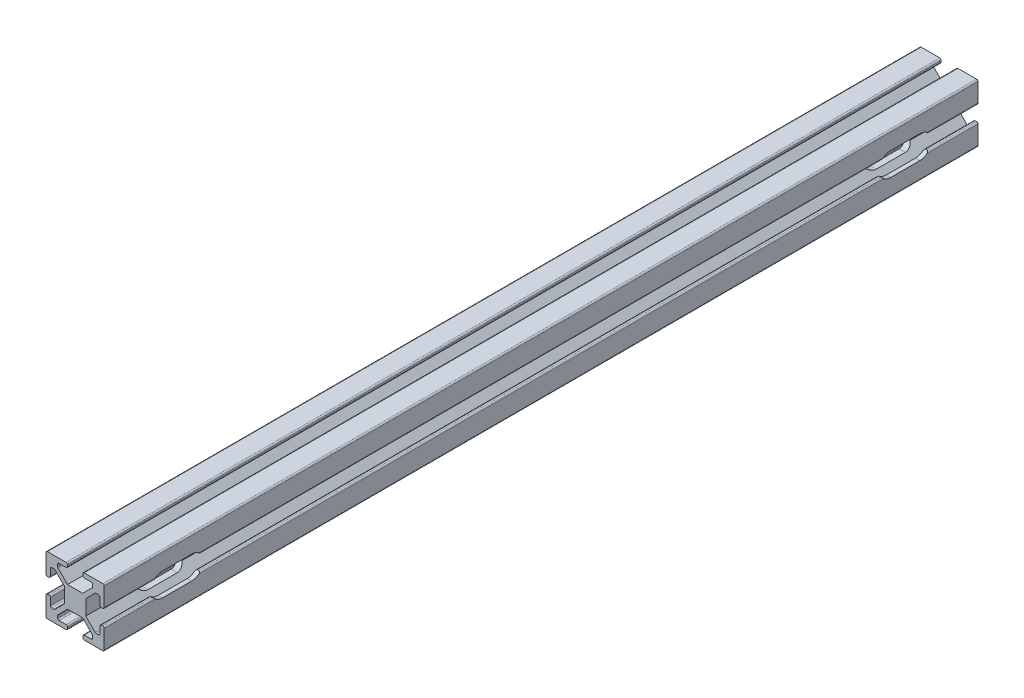
SolidWorks part; units mm, degrees
material "6061 Alloy"
ref_plane "Front Plane" through (0, 0, 0) normal (0, 0, 1) x (1, 0, 0)
ref_plane "Top Plane" through (0, 0, 0) normal (0, 1, 0) x (1, 0, 0)
ref_plane "Right Plane" through (0, 0, 0) normal (1, 0, 0) x (0, 0, -1)
sketch "Sketch1" plane through (0, 0, 0) normal (0, 0, 1) x (1, 0, 0)
  line L0 (-10, 2.63) -> (-10, 10)
  line L1 (-10, 10) -> (-2.63, 10)
  line L2 (-2.63, 10) -> (-2.63, 8.5)
  line L3 (-2.63, 8.5) -> (-5.995, 8.5)
  line L4 (-5.995, 8.5) -> (-5.995, 7.0557)
  line L5 (-5.995, 7.0557) -> (-2.5943, 3.655)
  line L6 (-2.5943, 3.655) -> (2.5943, 3.655)
  line L7 (0, 3.655) -> (0, 0) construction
  line L8 (0, 0) -> (-3.655, 0) construction
  line L9 (-3.655, -2.5943) -> (-3.655, 2.5943)
  line L10 (-3.655, 2.5943) -> (-7.0557, 5.995)
  line L11 (-7.0557, 5.995) -> (-8.5, 5.995)
  line L12 (-8.5, 5.995) -> (-8.5, 2.63)
  line L13 (-8.5, 2.63) -> (-10, 2.63)
  line L14 (8.5, 2.63) -> (10, 2.63)
  line L15 (8.5, 5.995) -> (8.5, 2.63)
  line L16 (7.0557, 5.995) -> (8.5, 5.995)
  line L17 (3.655, 2.5943) -> (7.0557, 5.995)
  line L18 (3.655, -2.5943) -> (3.655, 2.5943)
  line L19 (5.995, 7.0557) -> (2.5943, 3.655)
  line L20 (5.995, 8.5) -> (5.995, 7.0557)
  line L21 (2.63, 8.5) -> (5.995, 8.5)
  line L22 (2.63, 10) -> (2.63, 8.5)
  line L23 (10, 10) -> (2.63, 10)
  line L24 (10, 2.63) -> (10, 10)
  line L25 (10, -2.63) -> (10, -10)
  line L26 (10, -10) -> (2.63, -10)
  line L27 (2.63, -10) -> (2.63, -8.5)
  line L28 (2.63, -8.5) -> (5.995, -8.5)
  line L29 (5.995, -8.5) -> (5.995, -7.0557)
  line L30 (5.995, -7.0557) -> (2.5943, -3.655)
  line L31 (3.655, -2.5943) -> (7.0557, -5.995)
  line L32 (7.0557, -5.995) -> (8.5, -5.995)
  line L33 (8.5, -5.995) -> (8.5, -2.63)
  line L34 (8.5, -2.63) -> (10, -2.63)
  line L35 (-8.5, -2.63) -> (-10, -2.63)
  line L36 (-8.5, -5.995) -> (-8.5, -2.63)
  line L37 (-7.0557, -5.995) -> (-8.5, -5.995)
  line L38 (-3.655, -2.5943) -> (-7.0557, -5.995)
  line L39 (-2.5943, -3.655) -> (2.5943, -3.655)
  line L40 (-5.995, -7.0557) -> (-2.5943, -3.655)
  line L41 (-5.995, -8.5) -> (-5.995, -7.0557)
  line L42 (-2.63, -8.5) -> (-5.995, -8.5)
  line L43 (-2.63, -10) -> (-2.63, -8.5)
  line L44 (-10, -10) -> (-2.63, -10)
  line L45 (-10, -2.63) -> (-10, -10)
  point P41 (3.655, 0)
  dimension "D1" = 20
  dimension "D2" = 20
  dimension "D3" = 5.26
  dimension "D4" = 11.99
  dimension "D5" = 1.5
  dimension "D6" = 1.5
  dimension "D7" = 7.31
extrude "Boss-Extrude1" add sketch "Sketch1" against normal blind 300
fillet "Fillet1" radius 0.5 36 edges at (10, 10, -150) (7.0557, 5.995, -150) (8.5, 2.63, -150) (10, 2.63, -150) (8.5, 5.995, -150) (2.63, 10, -150) (2.63, 8.5, -150) (5.995, 8.5, -150) (5.995, 7.0557, -150) (10, -10, -150) (10, -2.63, -150) (8.5, -2.63, -150) (8.5, -5.995, -150) (7.0557, -5.995, -150) (5.995, -7.0557, -150) (5.995, -8.5, -150) (2.63, -8.5, -150) (2.63, -10, -150) (-10, -10, -150) (-2.63, -10, -150) (-2.63, -8.5, -150) (-5.995, -8.5, -150) (-5.995, -7.0557, -150) (-7.0557, -5.995, -150) (-8.5, -5.995, -150) (-10, -2.63, -150) (-8.5, -2.63, -150) (-7.0557, 5.995, -150) (-10, 10, -150) (-10, 2.63, -150) (-8.5, 2.63, -150) (-8.5, 5.995, -150) (-5.995, 8.5, -150) (-5.995, 7.0557, -150) (-2.63, 8.5, -150) (-2.63, 10, -150)
sketch "Sketch2" plane through (0, 0, 0) normal (1, 0, 0) x (0, 0, -1)
  line L0 (150, 9.5) -> (150, -9.5) construction
  line L1 (300, 9.5) -> (0, 9.5) construction
  line L2 (0, -9.5) -> (300, -9.5) construction
  line L3 (20, 4) -> (30, 4)
  line L4 (20, -4) -> (30, -4)
  line L5 (280, 4) -> (270, 4)
  line L6 (280, -4) -> (270, -4)
  arc A0 (20, 4) -> (20, -4) centre (20, 0) ccw
  arc A2 (30, -4) -> (30, 4) centre (30, 0) ccw
  arc A3 (280, 4) -> (280, -4) centre (280, 0) cw
  arc A4 (270, -4) -> (270, 4) centre (270, 0) cw
  dimension "D1" = 8
  dimension "D2" = 20
  dimension "D3" = 10
extrude "Cut-Extrude1" cut sketch "Sketch2" against normal through all both and the other way through all
sketch "Sketch3" [suppressed] plane through (0, 0, 0) normal (0, 1, 0) x (1, 0, 0)
  line L0 (9.5, 0) -> (9.5, 300) construction
  circle A0 centre (0, 150) radius 1.75
  point P6 (9.5, 150)
  dimension "D1" = 3.5
extrude "Cut-Extrude2" [suppressed] cut sketch "Sketch3" against normal through all both and the other way through all
